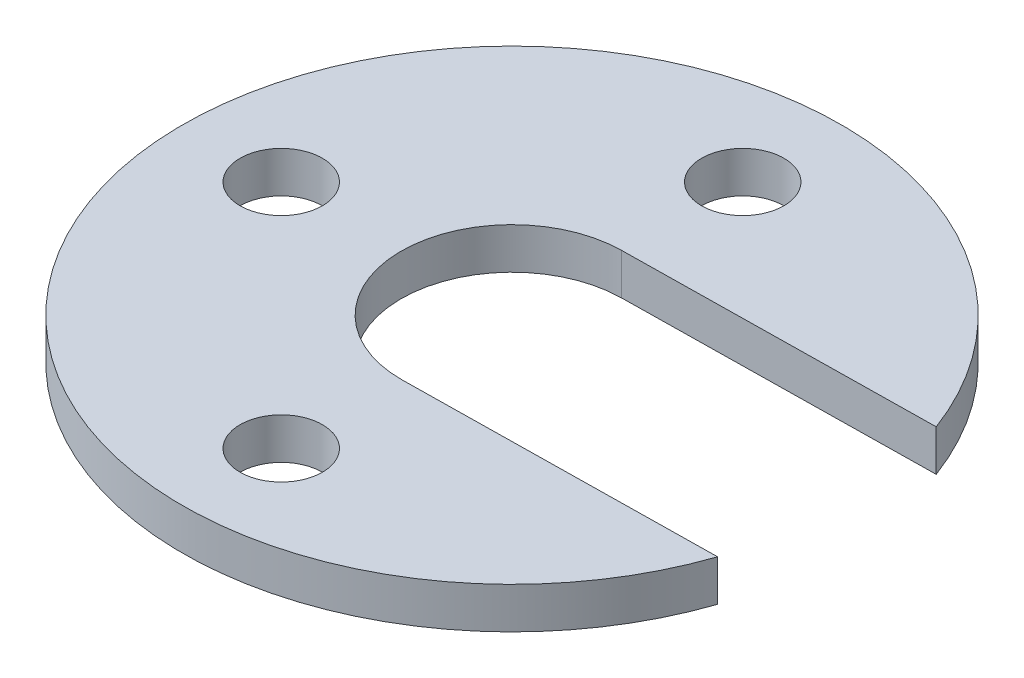
SolidWorks part; units mm, degrees
ref_plane "Front Plane" through (0, 0, 0) normal (0, 0, 1) x (1, 0, 0)
ref_plane "Top Plane" through (0, 0, 0) normal (0, 1, 0) x (1, 0, 0)
ref_plane "Right Plane" through (0, 0, 0) normal (1, 0, 0) x (0, 0, -1)
sketch "Sketch1" plane through (0, 0, 0) normal (0, 1, 0) x (1, 0, 0)
  line L0 (0, 0) -> (0, 41.8654) construction
  line L1 (0, 0) -> (43.8793, 0) construction
  line L2 (0, 0) -> (49.9822, 0.7323) construction
  line L3 (-0.1973, 13.4627) -> (37.4646, 14.0145)
  line L4 (0.1973, -13.4627) -> (37.8591, -12.9109)
  arc A0 (40, 0) -> (39.9957, 0.586) centre (0, 0) ccw
  circle A2 centre (0, 28) radius 5
  circle A3 centre (-28, 0) radius 5
  circle A4 centre (0, -28) radius 5
  arc A5 (-0.1973, 13.4627) -> (0.1973, -13.4627) centre (0, 0) ccw
  arc A7 (37.4646, 14.0145) -> (37.8591, -12.9109) centre (0, 0) ccw
  point P13 (24.9911, 0.3662)
  dimension "D1" = 80
  dimension "D2" = 10
  dimension "D4" = 10
  dimension "D5" = 10
  dimension "D3" = 28
  dimension "D6" = 28
  dimension "D7" = 28
extrude "Boss-Extrude1" add sketch "Sketch1" along normal blind 5 contours L3 A7 L4 A5 A2 A3 A4
